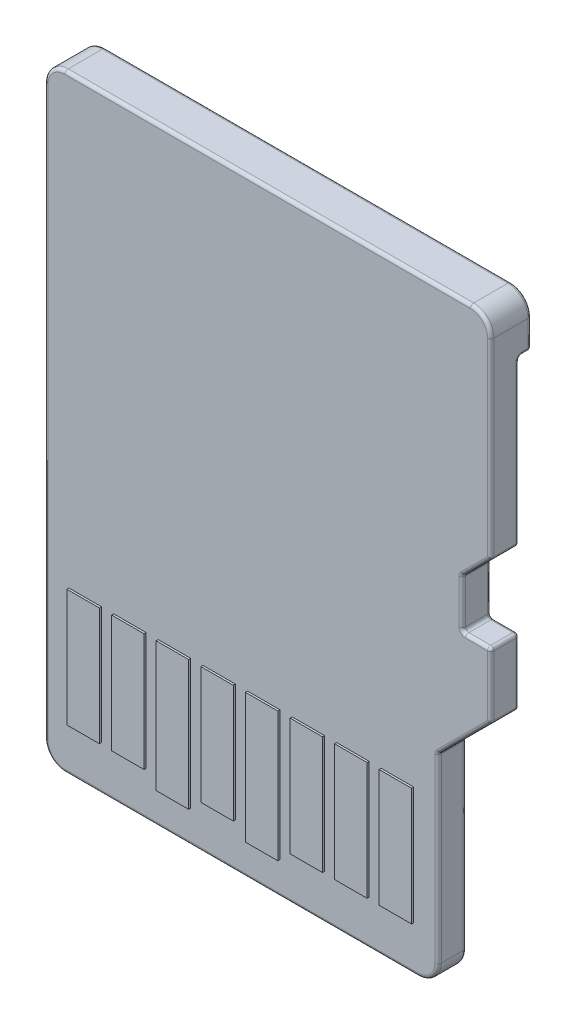
SolidWorks part; units mm, degrees
ref_plane "Front Plane" through (0, 0, 0) normal (0, 0, 1) x (1, 0, 0)
ref_plane "Top Plane" through (0, 0, 0) normal (0, 1, 0) x (1, 0, 0)
ref_plane "Right Plane" through (0, 0, 0) normal (1, 0, 0) x (0, 0, -1)
sketch "Sketch1" plane through (0, 0, 0) normal (0, 0, 1) x (1, 0, 0)
  line L0 (-5.5, 30.2306) -> (5.5, 30.2306)
  line L6 (-5.5, 15.2306) -> (-5.5, 30.2306)
  line L8 (5.5, 30.2306) -> (5.5, 21.5306)
  line L9 (5.5, 21.5306) -> (4.2, 20.2306)
  line L10 (4.2, 20.2306) -> (4.2, 15.2306)
  line L11 (4.2, 15.2306) -> (-5.5, 15.2306)
extrude "Boss-Extrude1" add sketch "Sketch1" against normal blind 0.6 and the other way blind 0.1
sketch "Sketch2" plane through (0, 0, -0.6) normal (0, 0, -1) x (-1, 0, 0)
  line L1 (-5.5, 30.2306) -> (5.5, 30.2306)
  line L5 (-5.5, 30.2306) -> (-5.5, 29.0306)
  line L6 (5.5, 29.0306) -> (5.5, 30.2306)
  arc A0 (-5.5, 29.0306) -> (5.5, 29.0306) centre (0, 53.9389) ccw
  dimension "D2" = 1.2
extrude "Boss-Extrude2" add sketch "Sketch2" along normal blind 0.3
sketch "Sketch3" plane through (0, 0, 0.1) normal (0, 0, 1) x (1, 0, 0)
  line L0 (-0.65, 15.2306) -> (-0.65, 30.2306) construction
  line L1 (-5.5, 15.2306) -> (4.2, 15.2306) construction
  line L2 (5.5, 30.2306) -> (-5.5, 30.2306) construction
  line L3 (-4.5, 16.3306) -> (3.2, 16.3306) construction
  line L4 (1.9068, 15.2306) -> (1.9068, 16.3306) construction
  line L5 (3.0193, 16.3306) -> (3.0193, 16.0306) construction
  line L6 (-4.9, 19.2306) -> (-4.9, 16.3306)
  line L15 (-4.9, 19.2306) -> (-4.1, 19.2306)
  line L16 (-4.1, 19.2306) -> (-4.1, 16.3306)
  line L17 (-4.9, 16.3306) -> (-4.1, 16.3306)
  line L18 (2.8, 19.2306) -> (2.8, 16.3306)
  line L19 (2.8, 19.2306) -> (3.6, 19.2306)
  line L20 (3.6, 19.2306) -> (3.6, 16.3306)
  line L21 (2.8, 16.3306) -> (3.6, 16.3306)
  line L22 (-4.5, 17.7806) -> (-3.4, 17.7806) construction
  line L23 (-3.4, 17.7806) -> (-2.3, 17.7806) construction
  line L24 (-2.3, 17.7806) -> (-1.2, 17.7806) construction
  line L25 (-1.2, 17.7806) -> (-0.1, 17.7806) construction
  line L26 (-0.1, 17.7806) -> (1, 17.7806) construction
  line L27 (1, 17.7806) -> (2.1, 17.7806) construction
  line L28 (2.1, 17.7806) -> (3.2, 17.7806) construction
  line L29 (-3.8, 19.2306) -> (-3, 19.2306)
  line L30 (-3.8, 19.2306) -> (-3.8, 16.3306)
  line L31 (-3.8, 16.3306) -> (-3, 16.3306)
  line L32 (-3, 19.2306) -> (-3, 16.3306)
  line L33 (-1.6, 19.2306) -> (-0.8, 19.2306)
  line L34 (-1.6, 19.2306) -> (-1.6, 16.3306)
  line L35 (-1.6, 16.3306) -> (-0.8, 16.3306)
  line L36 (-0.8, 19.2306) -> (-0.8, 16.3306)
  line L37 (0.6, 19.2306) -> (1.4, 19.2306)
  line L38 (0.6, 19.2306) -> (0.6, 16.3306)
  line L39 (0.6, 16.3306) -> (1.4, 16.3306)
  line L40 (1.4, 19.2306) -> (1.4, 16.3306)
  line L41 (1.7, 19.2306) -> (2.5, 19.2306)
  line L42 (1.7, 19.2306) -> (1.7, 16.3306)
  line L43 (1.7, 16.3306) -> (2.5, 16.3306)
  line L44 (2.5, 19.2306) -> (2.5, 16.3306)
  line L45 (3.2, 16.0306) -> (-4.5, 16.0306) construction
  line L46 (-2.7, 19.2306) -> (-1.9, 19.2306)
  line L47 (-2.7, 19.2306) -> (-2.7, 16.0306)
  line L48 (-2.7, 16.0306) -> (-1.9, 16.0306)
  line L49 (-1.9, 19.2306) -> (-1.9, 16.0306)
  line L50 (-0.5, 19.2306) -> (0.3, 19.2306)
  line L51 (-0.5, 19.2306) -> (-0.5, 16.0306)
  line L52 (-0.5, 16.0306) -> (0.3, 16.0306)
  line L53 (0.3, 19.2306) -> (0.3, 16.0306)
  dimension "D1" = 7.7
  dimension "D2" = 1.1
  dimension "D3" = 0.3
extrude "Boss-Extrude3" add sketch "Sketch3" along normal blind 0.05
sketch "Sketch4" plane through (0, 0, -0.6) normal (0, 0, -1) x (-1, 0, 0)
  line L0 (-5.5, 23.1306) -> (-5.5, 25.0306)
  line L1 (-4.8, 23.1306) -> (-5.5, 23.1306)
  line L5 (-4.8, 24.3306) -> (-4.8, 23.1306)
  line L6 (-4.8, 24.3306) -> (-5.5, 25.0306)
  point P1 (0, 0)
extrude "Cut-Extrude1" cut sketch "Sketch4" against normal up to surface (0.7 mm away) up to face at (-2.3, 17.6306, 0.1)
fillet "Fillet1" radius 0.5 4 edges at (5.5, 30.2306, -0.4) (-5.5, 30.2306, -0.4) (-5.5, 15.2306, -0.25) (4.2, 15.2306, -0.25)
fillet "Fillet2" radius 0.08 40 edges at (5.5, 29.0306, -0.75) (-5.5, 29.0306, -0.75) (5.15, 23.1306, 0.1) (5.5, 27.3806, 0.1) (5.3536, 30.0841, 0.1) (0, 30.2306, 0.1) (-5.3536, 30.0841, 0.1) (-5.5, 22.7306, 0.1) (-5.3536, 15.377, 0.1) (-0.65, 15.2306, 0.1) (4.0536, 15.377, 0.1) (-5.3536, 30.0841, -0.9) (-5.5, 29.3806, -0.9) (0, 28.4306, -0.9) (5.5, 29.3806, -0.9) (5.3536, 30.0841, -0.9) (0, 30.2306, -0.9) (4.0536, 15.377, -0.6) (4.2, 17.9806, -0.6) (4.85, 20.8806, -0.6) (5.5, 22.3306, -0.6) (5.15, 23.1306, -0.6) (4.8, 23.7306, -0.6) (5.15, 24.6806, -0.6) (5.5, 27.0306, -0.6) (0, 28.4306, -0.6) (-5.5, 22.3806, -0.6) (-5.3536, 15.377, -0.6) (-0.65, 15.2306, -0.6) (5.15, 24.6806, 0.1) (4.8, 23.7306, 0.1) (5.5, 22.3306, 0.1) (4.85, 20.8806, 0.1) (4.2, 17.9806, 0.1) (4.2, 20.2306, -0.25) (5.5, 21.5306, -0.25) (5.5, 25.0306, -0.25) (4.8, 24.3306, -0.25) (4.8, 23.1306, -0.25) (5.5, 23.1306, -0.25)
